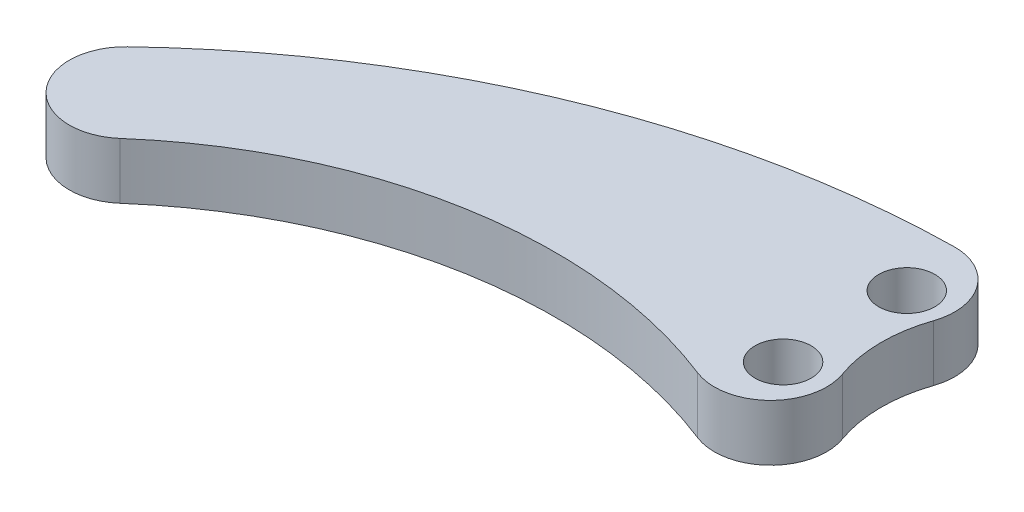
SolidWorks part; units mm, degrees
ref_plane "Front Plane" through (0, 0, 0) normal (0, 0, 1) x (1, 0, 0)
ref_plane "Top Plane" through (0, 0, 0) normal (0, 1, 0) x (1, 0, 0)
ref_plane "Right Plane" through (0, 0, 0) normal (1, 0, 0) x (0, 0, -1)
sketch "Sketch1" plane through (0, 0, 0) normal (0, 1, 0) x (1, 0, 0)
  line L0 (0, 22) -> (0, 0) construction
  circle A0 centre (0, 0) radius 5
  circle A1 centre (0, 22) radius 5
  arc A2 (10.2286, 26.0467) -> (0, 33) centre (0, 22) ccw
  arc A3 (-4.1768, -9.9831) -> (10.4438, -2.8349) centre (0, 0) ccw
  arc A4 (-106.8966, -9.7586) -> (-93.4115, -24.5227) centre (-100, -17) ccw
  arc A5 (-93.4115, -24.5227) -> (-4.1768, -9.9831) centre (-37.1412, -88.7717) cw
  arc A6 (-106.8966, -9.7586) -> (0, 33) centre (0, -122) cw
  arc A7 (10.4438, -2.8349) -> (10.2286, 26.0467) centre (30.5035, 11.7561) cw
  point P5 (0, 6.1)
  dimension "D1" = 10
  dimension "D4" = 20
  dimension "D2" = 22
  dimension "D3" = 100
  dimension "D5" = 17
  dimension "D6" = 33
extrude "Boss-Extrude1" add sketch "Sketch1" along normal blind 10
fillet "Fillet1" radius 10 2 edges at (10.4438, 5, 2.8349) (10.2286, 5, -26.0467)
